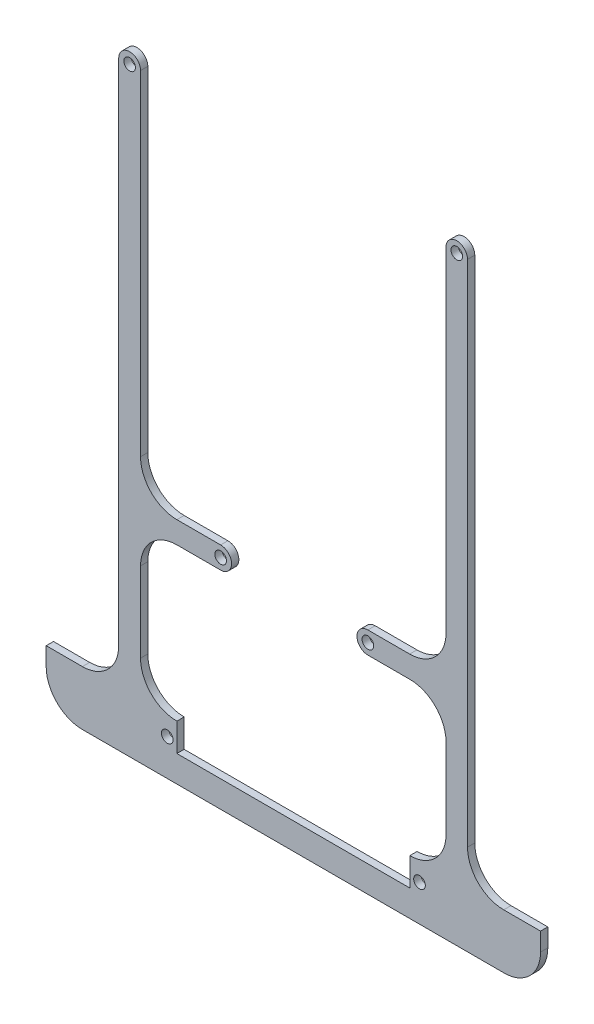
SolidWorks part; units mm, degrees
ref_plane "Front Plane" through (0, 0, 0) normal (0, 0, 1) x (1, 0, 0)
ref_plane "Top Plane" through (0, 0, 0) normal (0, 1, 0) x (1, 0, 0)
ref_plane "Right Plane" through (0, 0, 0) normal (1, 0, 0) x (0, 0, -1)
sketch "Sketch1" plane through (0, 0, 0) normal (0, 0, 1) x (1, 0, 0)
  line L0 (-48.0442, 75) -> (-48.0442, -65)
  line L5 (0, -75) -> (0, 75) construction
  line L6 (45, 0) -> (-45, 0) construction
  line L7 (-42.0442, 75) -> (-42.0442, -17)
  line L8 (42, 75) -> (42, -17)
  line L9 (47.9116, 75) -> (47.9116, -65.0442)
  line L10 (-58.0442, -75) -> (-68, -75)
  line L11 (57.8674, -75) -> (68, -75)
  line L12 (-68, -75) -> (-68, -80)
  line L13 (-58, -90) -> (58, -90)
  line L14 (68, -80) -> (68, -75)
  line L16 (0, -75) -> (0, -80) construction
  line L17 (-34.7, -80) -> (-32.0442, -80)
  line L20 (-12.352, -75) -> (-12.352, -82.72) construction
  line L21 (-32.0442, -75) -> (-32.0442, -82.72)
  line L22 (-45, 0) -> (-20, 0) construction
  line L23 (-20, 0) -> (-20, -30) construction
  line L24 (-20, -30) -> (20.5, -30) construction
  line L25 (-20, -27) -> (-32.0442, -27)
  line L26 (-20, -33) -> (-32.0442, -33)
  line L27 (-42.0442, -43) -> (-42.0442, -65)
  line L28 (20.5, -27) -> (32, -27)
  line L29 (20.5, -33) -> (32.0442, -33)
  line L30 (42, -42.9558) -> (42, -65.0442)
  line L31 (-32.0442, -82.72) -> (32.0442, -82.72)
  line L32 (32.0442, -82.72) -> (32.0442, -75)
  line L33 (32.0442, -80) -> (34.7, -80)
  circle A0 centre (-45.0442, 75) radius 1.6
  circle A1 centre (44.9558, 75) radius 1.6
  arc A2 (-42.0442, 75) -> (-48.0442, 75) centre (-45.0442, 75) ccw
  arc A3 (47.9116, 75) -> (42, 75) centre (44.9558, 75) ccw
  arc A4 (-58, -90) -> (-68, -80) centre (-58, -80) cw
  arc A5 (58, -90) -> (68, -80) centre (58, -80) ccw
  circle A6 centre (-34.7, -80) radius 1.6
  circle A7 centre (34.7, -80) radius 1.6
  circle A8 centre (-20, -30) radius 1.6
  arc A9 (-20, -33) -> (-20, -27) centre (-20, -30) ccw
  circle A10 centre (20.5, -30) radius 1.6
  arc A11 (20.5, -27) -> (20.5, -33) centre (20.5, -30) ccw
  arc A12 (-32.0442, -75) -> (-42.0442, -65) centre (-32.0442, -65) cw
  arc A13 (-58.0442, -75) -> (-48.0442, -65) centre (-58.0442, -65) ccw
  arc A14 (-32.0442, -33) -> (-42.0442, -43) centre (-32.0442, -43) ccw
  arc A15 (-32.0442, -27) -> (-42.0442, -17) centre (-32.0442, -17) cw
  arc A16 (32, -27) -> (42, -17) centre (32, -17) ccw
  arc A17 (42, -42.9558) -> (32.0442, -33) centre (32.0442, -42.9558) ccw
  arc A18 (57.8674, -75) -> (47.9116, -65.0442) centre (57.8674, -65.0442) cw
  arc A19 (32.0442, -75) -> (42, -65.0442) centre (32.0442, -65.0442) ccw
  point P0 (0, 0)
  point P20 (-68, -90)
  point P26 (0, -75)
  point P28 (0, -80)
  point P50 (-42.0442, -33)
  point P57 (42, -33)
  dimension "D3" = 10
  dimension "D1" = 15
  dimension "D4" = 10
  dimension "D6" = 10
  dimension "D5" = 10
  dimension "D7" = 10
  dimension "D8" = 10
  dimension "D9" = 10
  dimension "D10" = 9.9558
  dimension "D11" = 9.9558
  dimension "D12" = 9.9558
  dimension "D2" = 90
  dimension "D13" = 69.4
  dimension "D14" = 40.5
extrude "Boss-Extrude1" add sketch "Sketch1" along normal blind 2
